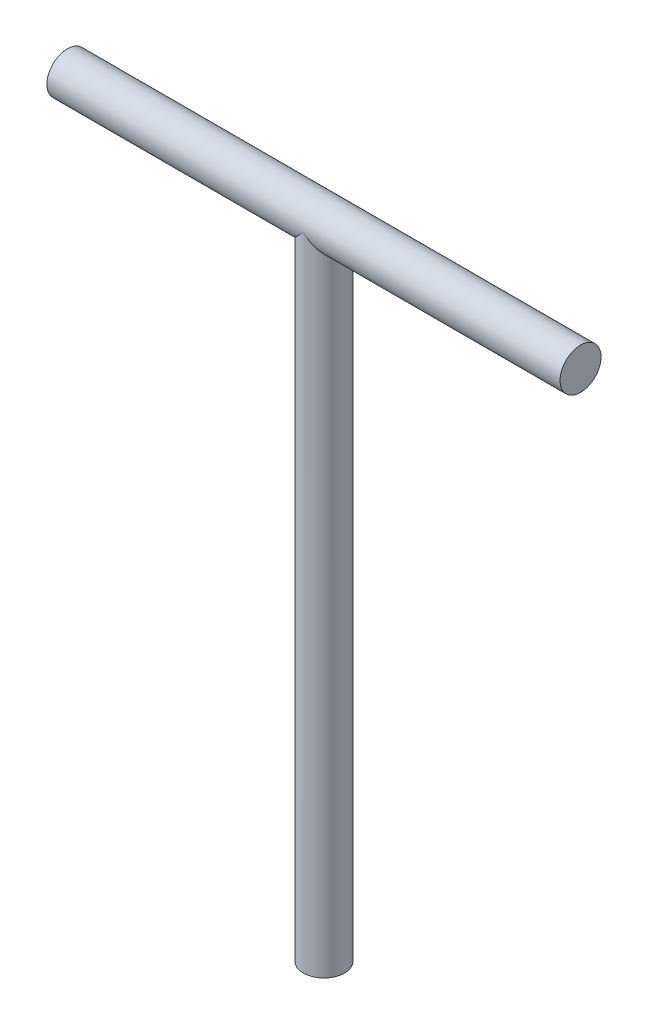
SolidWorks part; units mm, degrees
ref_plane "Front Plane" through (0, 0, 0) normal (0, 0, 1) x (1, 0, 0)
ref_plane "Top Plane" through (0, 0, 0) normal (0, 1, 0) x (1, 0, 0)
ref_plane "Right Plane" through (0, 0, 0) normal (1, 0, 0) x (0, 0, -1)
sketch "Sketch1" plane through (0, 0, 0) normal (1, 0, 0) x (0, 0, -1)
  circle A0 centre (0, 0) radius 16
  dimension "D1" = 32
extrude "Boss-Extrude1" add sketch "Sketch1" along normal blind 400
sketch "Sketch2" plane through (0, 0, 0) normal (0, 1, 0) x (1, 0, 0)
  line L0 (-53.0469, 0) -> (453.0469, 0) construction
  line L1 (200, 16) -> (200, -16) construction
  line L2 (400, 16) -> (0, 16) construction
  circle A0 centre (200, 0) radius 16
  dimension "D1" = 32
extrude "Boss-Extrude2" add sketch "Sketch2" against normal blind 500
